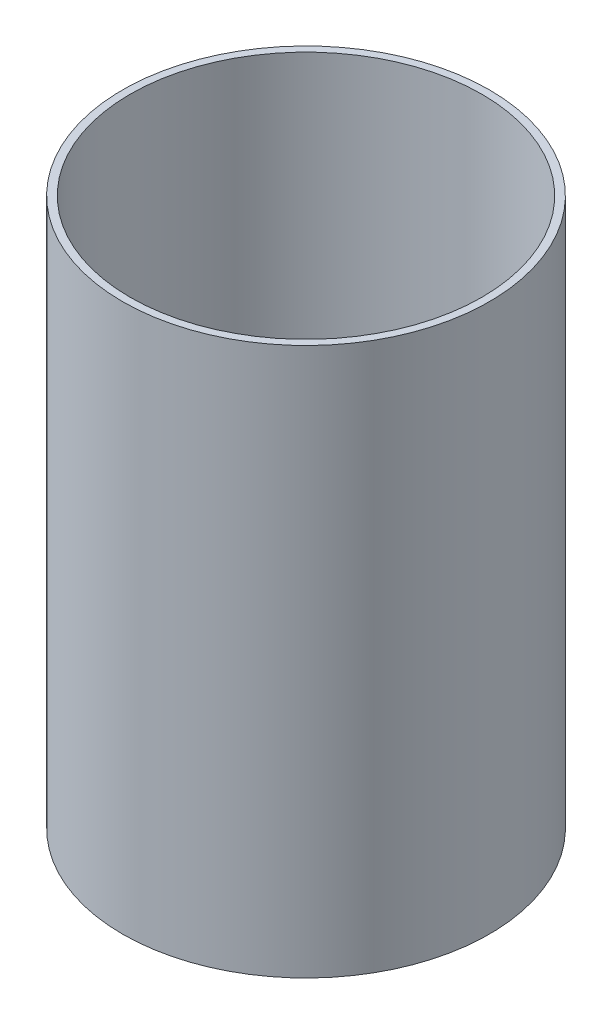
SolidWorks part; units mm, degrees
material "Fonte grise"
ref_plane "Plan de face" through (0, 0, 0) normal (0, 0, 1) x (1, 0, 0)
ref_plane "Plan de dessus" through (0, 0, 0) normal (0, 1, 0) x (1, 0, 0)
ref_plane "Plan de droite" through (0, 0, 0) normal (1, 0, 0) x (0, 0, -1)
sketch "Esquisse1" plane through (0, 0, 0) normal (0, 1, 0) x (1, 0, 0)
  circle A0 centre (0, 0) radius 36.5
  dimension "D1" = 73
extrude "Boss.-Extru.1" add sketch "Esquisse1" along normal blind 109
shell "Coque1" thickness 1.5
